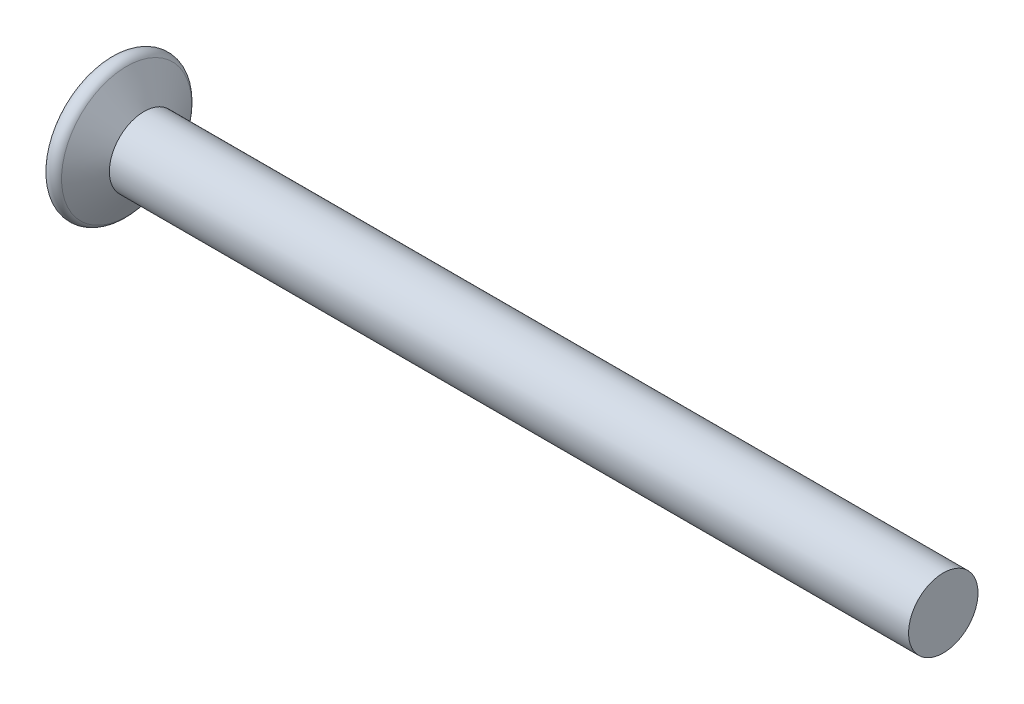
SolidWorks part; units mm, degrees
ref_plane "Plano frontal" through (0, 0, 0) normal (0, 0, 1) x (1, 0, 0)
ref_plane "Plano superior" through (0, 0, 0) normal (0, 1, 0) x (1, 0, 0)
ref_plane "Plano direito" through (0, 0, 0) normal (1, 0, 0) x (0, 0, -1)
sketch "Esboço1" plane through (0, 0, 0) normal (0, 1, 0) x (1, 0, 0)
  line L0 (0, 1.25) -> (0, 2.5) construction
  line L1 (0, 2.5) -> (0.5, 2.5) construction
  line L2 (0.5, 2.5) -> (1.2217, 1.25) construction
  line L3 (1.2217, 1.25) -> (30, 1.25)
  line L4 (30, 1.25) -> (30, 0)
  line L5 (30, 0) -> (1.25, 0)
  line L6 (0, 0) -> (-13.2091, 0) construction
  line L7 (0, 1.25) -> (1.25, 0)
  line L8 (0.5915, 2.3415) -> (1.2217, 1.25)
  line L9 (0, 2.183) -> (0, 1.25)
  arc A0 (0.5915, 2.3415) -> (0, 2.183) centre (0.317, 2.183) ccw
  point P13 (-0.0583, 1.1091)
  dimension "D1" = 30
  dimension "D2" = 2.5
  dimension "D3" = 2.5
  dimension "D4" = 0.5
  dimension "D5" = 60
  dimension "D6" = 45
  dimension "D7" = 2.5
revolve "Revolução1" add sketch "Esboço1" angle 360 about L6
sketch "Esboço2" plane through (0, 0, 0) normal (1, 0, 0) x (0, 0, -1)
  line L0 (0, 1.25) -> (0, -1.25) construction
  line L1 (1.25, 0) -> (-1.25, 0) construction
  line L2 (-0.3, 1.25) -> (-0.3, -1.25) construction
  line L3 (0.3, 1.25) -> (0.3, -1.25) construction
  line L4 (1.25, 0.3) -> (-1.25, 0.3) construction
  line L5 (1.25, -0.3) -> (-1.25, -0.3) construction
  line L6 (-0.3, 1.2135) -> (-0.3, 0.6)
  line L7 (-0.6, 0.3) -> (-1.2135, 0.3)
  circle A0 centre (0, 0) radius 1.25 construction
  arc A1 (-0.3, 0.6) -> (-0.6, 0.3) centre (-0.6, 0.6) cw
  arc A2 (-0.3, 1.2135) -> (-1.2135, 0.3) centre (-0.2169, 0.2169) ccw
  dimension "D5" = 0.3
  dimension "D1" = 0.3
  dimension "D2" = 0.3
  dimension "D3" = 0.3
  dimension "D4" = 0.3
extrude "Ressalto-extrusão1" add sketch "Esboço2" along normal blind 1
pattern_circular "PadrãoCircular1" count 4 over 360 about axis through (0, 0, 0) along (1, 0, 0) of "Ressalto-extrusão1"
